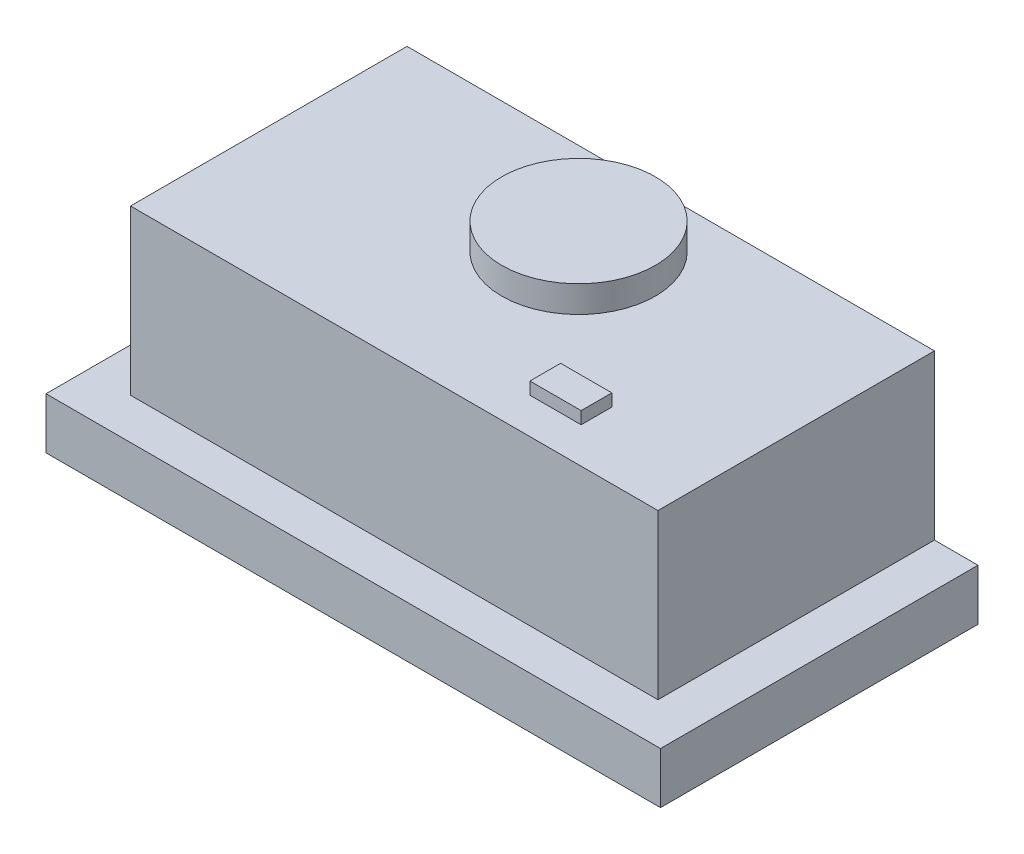
SolidWorks part; units mm, degrees
ref_plane "Front Plane" through (0, 0, 0) normal (0, 0, 1) x (1, 0, 0)
ref_plane "Top Plane" through (0, 0, 0) normal (0, 1, 0) x (1, 0, 0)
ref_plane "Right Plane" through (0, 0, 0) normal (1, 0, 0) x (0, 0, -1)
sketch "Sketch1" plane through (0, 0, 0) normal (0, 1, 0) x (1, 0, 0)
  line L1 (300, -155) -> (-300, -155)
  line L2 (300, -155) -> (300, 155)
  line L3 (300, 155) -> (-300, 155)
  line L4 (-300, -155) -> (-300, 155)
  line L5 (300, -155) -> (-300, 155) construction
  line L6 (300, 155) -> (-300, -155) construction
  point P0 (0, 0)
  dimension "D1" = 310
  dimension "D2" = 600
extrude "Boss-Extrude1" add sketch "Sketch1" along normal blind 50
sketch "Sketch2" plane through (0, 50, 0) normal (0, 1, 0) x (1, 0, 0)
  line L1 (300, 155) -> (-300, 155) construction
  line L2 (257.5, -115) -> (-257.5, -115)
  line L3 (257.5, -115) -> (257.5, 155)
  line L4 (257.5, 155) -> (-257.5, 155)
  line L5 (-257.5, -115) -> (-257.5, 155)
  line L6 (257.5, -115) -> (-257.5, 155) construction
  line L7 (257.5, 155) -> (-257.5, -115) construction
  point P0 (0, 20)
  dimension "D1" = 270
  dimension "D2" = 515
extrude "Boss-Extrude2" add sketch "Sketch2" along normal blind 160
sketch "Sketch3" plane through (0, 210, 0) normal (0, 1, 0) x (1, 0, 0)
  line L0 (257.5, 155) -> (-257.5, 155) construction
  circle A0 centre (0, 65) radius 75
  dimension "D1" = 150
  dimension "D2" = 90
extrude "Boss-Extrude3" add sketch "Sketch3" along normal blind 26
ref_plane "Plane1" through (147.5, 0, 0) normal (1, 0, 0) x (0, 0, -1)
sketch "Sketch4" plane through (147.5, 0, 0) normal (1, 0, 0) x (0, 0, -1)
  line L0 (-115, 210) -> (155, 210) construction
  line L1 (-80, 210) -> (-50, 210)
  line L2 (-80, 210) -> (-80, 222)
  line L3 (-80, 222) -> (-50, 222)
  line L4 (-50, 210) -> (-50, 222)
  line L5 (-115, 210) -> (-115, 50) construction
  dimension "D1" = 12
  dimension "D2" = 30
  dimension "D3" = 35
extrude "Boss-Extrude4" add sketch "Sketch4" against normal blind 50
